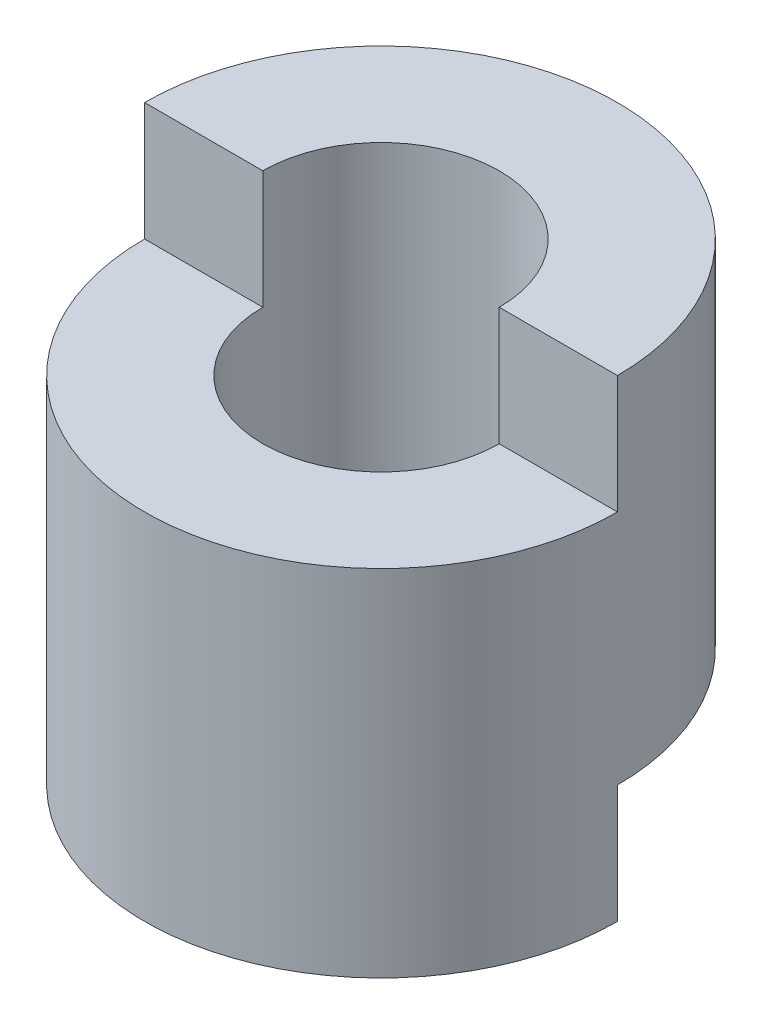
SolidWorks part; units mm, degrees
ref_plane "Front Plane" through (0, 0, 0) normal (0, 0, 1) x (1, 0, 0)
ref_plane "Top Plane" through (0, 0, 0) normal (0, 1, 0) x (1, 0, 0)
ref_plane "Right Plane" through (0, 0, 0) normal (1, 0, 0) x (0, 0, -1)
sketch "Sketch1" plane through (0, 0, 0) normal (0, 0, 1) x (1, 0, 0)
  line L1 (0, 0) -> (10, 0)
  line L2 (0, 0) -> (0, 20)
  line L3 (0, 20) -> (10, 20)
  line L4 (10, 0) -> (10, 20)
  dimension "D1" = 10
  dimension "D2" = 20
revolve "Revolve1" add sketch "Sketch1" angle 360 about L2
sketch "Sketch2" plane through (0, 20, 0) normal (0, 1, 0) x (1, 0, 0)
  circle A0 centre (0, 0) radius 5
  dimension "D1" = 10
extrude "Cut-Extrude1" cut sketch "Sketch2" against normal blind 20
sketch "Sketch3" plane through (0, 20, 0) normal (0, 1, 0) x (1, 0, 0)
  line L0 (-10, 0) -> (-5, 0)
  line L1 (5, 0) -> (10, 0)
  arc A0 (-10, 0) -> (10, 0) centre (0, 0) ccw
  circle A1 centre (0, 0) radius 10 construction
  arc A2 (-5, 0) -> (5, 0) centre (0, 0) ccw
  circle A3 centre (0, 0) radius 5 construction
  dimension "D3" = 5
  dimension "D4" = 10
  dimension "D1" = 5
  dimension "D2" = 5
extrude "Cut-Extrude2" cut sketch "Sketch3" against normal blind 5
sketch "Sketch4" plane through (0, 0, 0) normal (0, -1, 0) x (-1, 0, 0)
  line L0 (10, 0) -> (5, 0)
  line L1 (-5, 0) -> (-10, 0)
  arc A0 (10, 0) -> (-10, 0) centre (0, 0) ccw
  arc A1 (5, 0) -> (-5, 0) centre (0, 0) ccw
  circle A2 centre (0, 0) radius 5 construction
  dimension "D1" = 5
  dimension "D2" = 10
extrude "Cut-Extrude3" cut sketch "Sketch4" against normal blind 5
